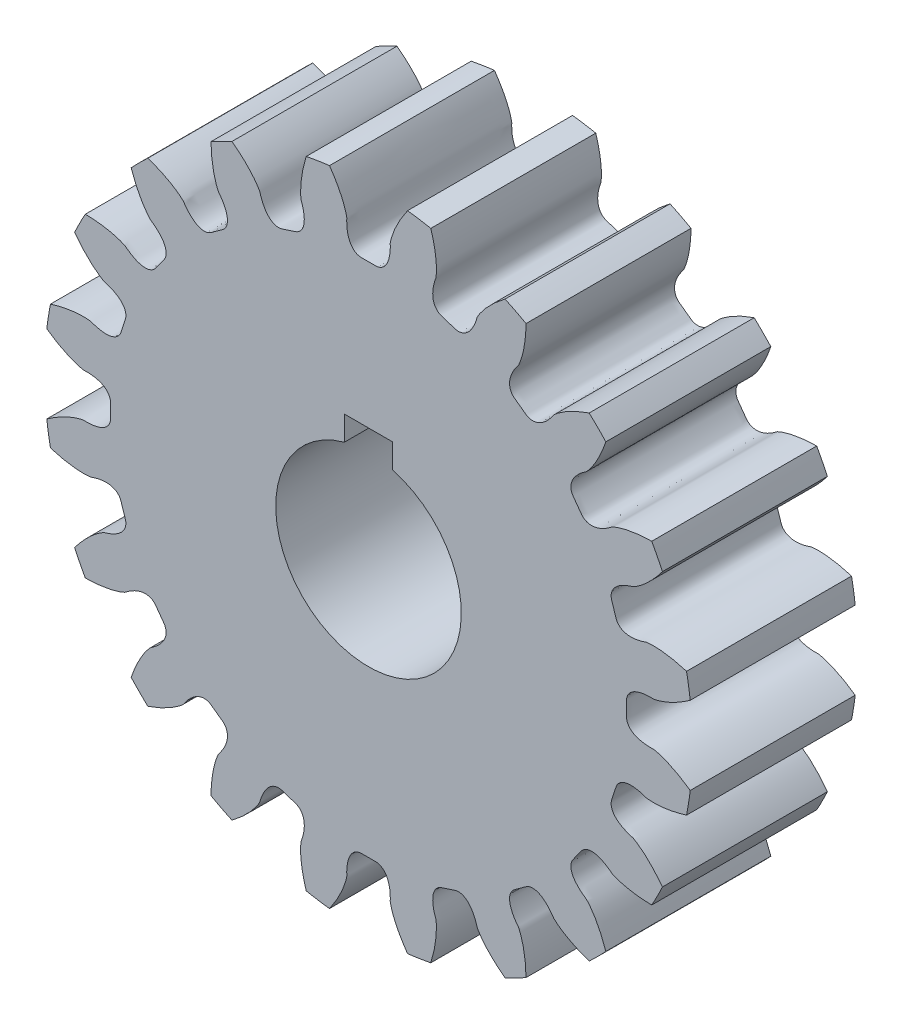
SolidWorks part; units mm, degrees
ref_plane "Front Plane" through (0, 0, 0) normal (0, 0, 1) x (1, 0, 0)
ref_plane "Top Plane" through (0, 0, 0) normal (0, 1, 0) x (1, 0, 0)
ref_plane "Right Plane" through (0, 0, 0) normal (1, 0, 0) x (0, 0, -1)
sketch "Sketch2" plane through (0, 0, 4.7625) normal (0, 0, 1) x (1, 0, 0)
  arc A20 (12.6697, 5.8856) -> (12.2086, 6.7905) centre (0, 0) ccw
  arc A21 (10.2308, 9.5127) -> (9.5127, 10.2308) centre (0, 0) ccw
  arc A22 (6.7905, 12.2086) -> (5.8856, 12.6697) centre (0, 0) ccw
  arc A23 (2.6855, 13.7094) -> (1.6824, 13.8683) centre (0, 0) ccw
  arc A24 (-1.6824, 13.8683) -> (-2.6855, 13.7094) centre (0, 0) ccw
  arc A25 (-5.8856, 12.6697) -> (-6.7905, 12.2086) centre (0, 0) ccw
  arc A26 (-9.5127, 10.2308) -> (-10.2308, 9.5127) centre (0, 0) ccw
  arc A27 (-12.2086, 6.7905) -> (-12.6697, 5.8856) centre (0, 0) ccw
  arc A28 (-13.7094, 2.6855) -> (-13.8683, 1.6824) centre (0, 0) ccw
  arc A29 (-13.8683, -1.6824) -> (-13.7094, -2.6855) centre (0, 0) ccw
  arc A30 (-12.6697, -5.8856) -> (-12.2086, -6.7905) centre (0, 0) ccw
  arc A31 (-10.2308, -9.5127) -> (-9.5127, -10.2308) centre (0, 0) ccw
  arc A32 (-6.7905, -12.2086) -> (-5.8856, -12.6697) centre (0, 0) ccw
  arc A33 (-2.6855, -13.7094) -> (-1.6824, -13.8683) centre (0, 0) ccw
  arc A34 (1.6824, -13.8683) -> (2.6855, -13.7094) centre (0, 0) ccw
  arc A35 (5.8856, -12.6697) -> (6.7905, -12.2086) centre (0, 0) ccw
  arc A36 (9.5127, -10.2308) -> (10.2308, -9.5127) centre (0, 0) ccw
  arc A37 (12.2086, -6.7905) -> (12.6697, -5.8856) centre (0, 0) ccw
  arc A38 (13.7094, -2.6855) -> (13.8683, -1.6824) centre (0, 0) ccw
  arc A39 (13.8683, 1.6824) -> (13.7094, 2.6855) centre (0, 0) ccw
  arc A40 (12.6697, 5.8856) -> (12.2086, 6.7905) centre (0, 0) ccw
  arc A41 (10.2308, 9.5127) -> (9.5127, 10.2308) centre (0, 0) ccw
  arc A42 (6.7905, 12.2086) -> (5.8856, 12.6697) centre (0, 0) ccw
  arc A43 (2.6855, 13.7094) -> (1.6824, 13.8683) centre (0, 0) ccw
  arc A44 (-1.6824, 13.8683) -> (-2.6855, 13.7094) centre (0, 0) ccw
  arc A45 (-5.8856, 12.6697) -> (-6.7905, 12.2086) centre (0, 0) ccw
  arc A46 (-9.5127, 10.2308) -> (-10.2308, 9.5127) centre (0, 0) ccw
  arc A47 (-12.2086, 6.7905) -> (-12.6697, 5.8856) centre (0, 0) ccw
  arc A48 (-13.7094, 2.6855) -> (-13.8683, 1.6824) centre (0, 0) ccw
  arc A49 (-13.8683, -1.6824) -> (-13.7094, -2.6855) centre (0, 0) ccw
  arc A50 (-12.6697, -5.8856) -> (-12.2086, -6.7905) centre (0, 0) ccw
  arc A51 (-10.2308, -9.5127) -> (-9.5127, -10.2308) centre (0, 0) ccw
  arc A52 (-6.7905, -12.2086) -> (-5.8856, -12.6697) centre (0, 0) ccw
  arc A53 (-2.6855, -13.7094) -> (-1.6824, -13.8683) centre (0, 0) ccw
  arc A54 (1.6824, -13.8683) -> (2.6855, -13.7094) centre (0, 0) ccw
  arc A55 (5.8856, -12.6697) -> (6.7905, -12.2086) centre (0, 0) ccw
  arc A56 (9.5127, -10.2308) -> (10.2308, -9.5127) centre (0, 0) ccw
  arc A57 (12.2086, -6.7905) -> (12.6697, -5.8856) centre (0, 0) ccw
  arc A58 (13.7094, -2.6855) -> (13.8683, -1.6824) centre (0, 0) ccw
  arc A59 (13.8683, 1.6824) -> (13.7094, 2.6855) centre (0, 0) ccw
  spline S20 degree 3 number of poles 85 (13.7094, 2.6855) -> (12.6697, 5.8856)
  spline S21 degree 3 number of poles 85 (12.2086, 6.7905) -> (10.2308, 9.5127)
  spline S22 degree 3 number of poles 85 (9.5127, 10.2308) -> (6.7905, 12.2086)
  spline S23 degree 3 number of poles 85 (5.8856, 12.6697) -> (2.6855, 13.7094)
  spline S24 degree 3 number of poles 85 (1.6824, 13.8683) -> (-1.6824, 13.8683)
  spline S25 degree 3 number of poles 85 (-2.6855, 13.7094) -> (-5.8856, 12.6697)
  spline S26 degree 3 number of poles 85 (-6.7905, 12.2086) -> (-9.5127, 10.2308)
  spline S27 degree 3 number of poles 85 (-10.2308, 9.5127) -> (-12.2086, 6.7905)
  spline S28 degree 3 number of poles 85 (-12.6697, 5.8856) -> (-13.7094, 2.6855)
  spline S29 degree 3 number of poles 85 (-13.8683, 1.6824) -> (-13.8683, -1.6824)
  spline S30 degree 3 number of poles 85 (-13.7094, -2.6855) -> (-12.6697, -5.8856)
  spline S31 degree 3 number of poles 85 (-12.2086, -6.7905) -> (-10.2308, -9.5127)
  spline S32 degree 3 number of poles 85 (-9.5127, -10.2308) -> (-6.7905, -12.2086)
  spline S33 degree 3 number of poles 85 (-5.8856, -12.6697) -> (-2.6855, -13.7094)
  spline S34 degree 3 number of poles 85 (-1.6824, -13.8683) -> (1.6824, -13.8683)
  spline S35 degree 3 number of poles 85 (2.6855, -13.7094) -> (5.8856, -12.6697)
  spline S36 degree 3 number of poles 85 (6.7905, -12.2086) -> (9.5127, -10.2308)
  spline S37 degree 3 number of poles 85 (10.2308, -9.5127) -> (12.2086, -6.7905)
  spline S38 degree 3 number of poles 85 (12.6697, -5.8856) -> (13.7094, -2.6855)
  spline S39 degree 3 number of poles 85 (13.8683, -1.6824) -> (13.8683, 1.6824)
  spline S40 degree 3 number of poles 85 (13.7094, 2.6855) -> (12.6697, 5.8856)
  spline S41 degree 3 number of poles 85 (12.2086, 6.7905) -> (10.2308, 9.5127)
  spline S42 degree 3 number of poles 85 (9.5127, 10.2308) -> (6.7905, 12.2086)
  spline S43 degree 3 number of poles 85 (5.8856, 12.6697) -> (2.6855, 13.7094)
  spline S44 degree 3 number of poles 85 (1.6824, 13.8683) -> (-1.6824, 13.8683)
  spline S45 degree 3 number of poles 85 (-2.6855, 13.7094) -> (-5.8856, 12.6697)
  spline S46 degree 3 number of poles 85 (-6.7905, 12.2086) -> (-9.5127, 10.2308)
  spline S47 degree 3 number of poles 85 (-10.2308, 9.5127) -> (-12.2086, 6.7905)
  spline S48 degree 3 number of poles 85 (-12.6697, 5.8856) -> (-13.7094, 2.6855)
  spline S49 degree 3 number of poles 85 (-13.8683, 1.6824) -> (-13.8683, -1.6824)
  spline S50 degree 3 number of poles 85 (-13.7094, -2.6855) -> (-12.6697, -5.8856)
  spline S51 degree 3 number of poles 85 (-12.2086, -6.7905) -> (-10.2308, -9.5127)
  spline S52 degree 3 number of poles 85 (-9.5127, -10.2308) -> (-6.7905, -12.2086)
  spline S53 degree 3 number of poles 85 (-5.8856, -12.6697) -> (-2.6855, -13.7094)
  spline S54 degree 3 number of poles 85 (-1.6824, -13.8683) -> (1.6824, -13.8683)
  spline S55 degree 3 number of poles 85 (2.6855, -13.7094) -> (5.8856, -12.6697)
  spline S56 degree 3 number of poles 85 (6.7905, -12.2086) -> (9.5127, -10.2308)
  spline S57 degree 3 number of poles 85 (10.2308, -9.5127) -> (12.2086, -6.7905)
  spline S58 degree 3 number of poles 85 (12.6697, -5.8856) -> (13.7094, -2.6855)
  spline S59 degree 3 number of poles 85 (13.8683, -1.6824) -> (13.8683, 1.6824)
  dimension "D1" = 0
extrude "Boss-Extrude2" add sketch "Sketch2" along normal blind 7.112
sketch "Sketch3" plane through (0, 0, 11.8745) normal (0, 0, 1) x (1, 0, 0)
  line L0 (0, -4) -> (0, 4.9154) construction
  line L1 (-1.0414, 4.9154) -> (1.0414, 4.9154)
  line L2 (1.0414, 4.9154) -> (1.0414, 3.8621)
  line L3 (-1.0414, 4.9154) -> (-1.0414, 3.8621)
  arc A0 (-1.0414, 3.8621) -> (1.0414, 3.8621) centre (0, 0) ccw
  point P8 (0, 4.9154)
  dimension "D1" = 8
  dimension "D2" = 8.9154
  dimension "D3" = 1.0414
extrude "Cut-Extrude1" cut sketch "Sketch3" against normal through all
